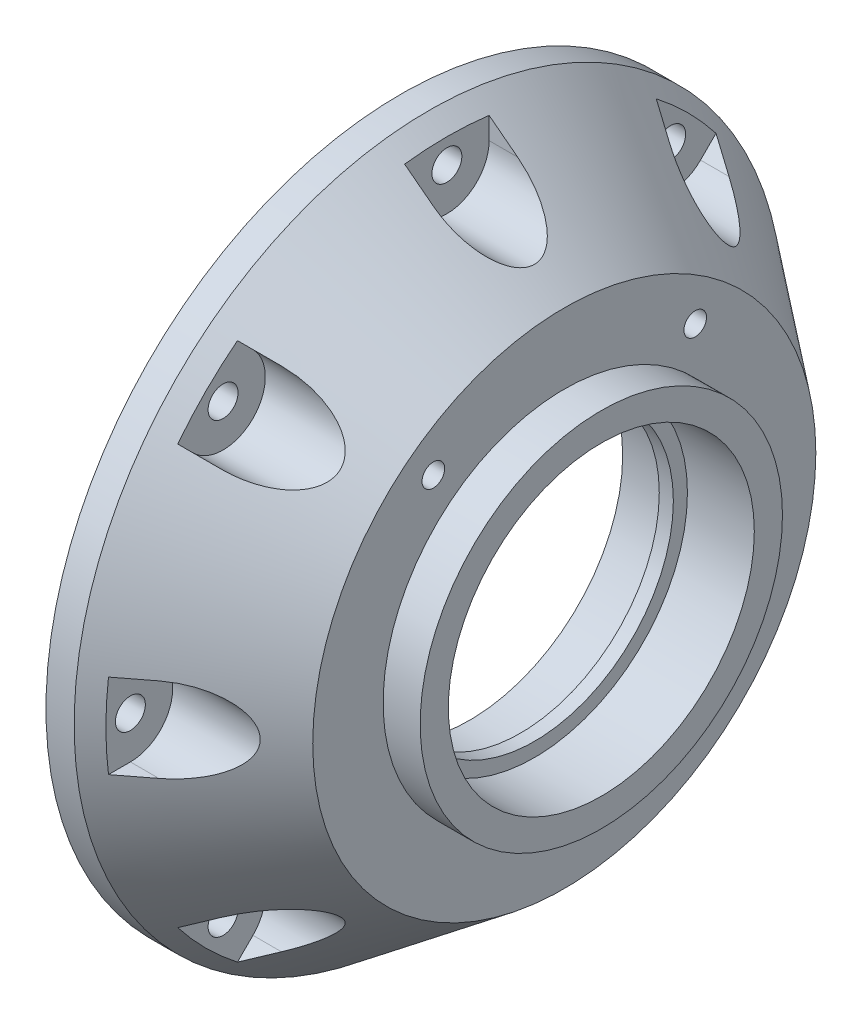
SolidWorks part; units mm, degrees
material "6061-T6 (SS)"
ref_plane "Front" through (0, 0, 0) normal (0, 0, 1) x (1, 0, 0)
ref_plane "Top" through (0, 0, 0) normal (0, 1, 0) x (1, 0, 0)
ref_plane "Right" through (0, 0, 0) normal (1, 0, 0) x (0, 0, -1)
sketch "Sketch1" plane through (0, 0, 0) normal (0, 0, 1) x (1, 0, 0)
  line L0 (462.4789, 312.41) -> (468.8289, 312.41)
  line L1 (462.4789, 312.41) -> (462.4789, 294.26)
  line L2 (462.4789, 152.41) -> (462.4789, 312.41) construction
  line L3 (462.4789, 294.26) -> (478.0364, 294.26)
  line L4 (478.0364, 294.26) -> (478.0364, 266.9159)
  line L5 (478.0364, 266.9159) -> (489.4664, 266.9159)
  line L6 (489.4664, 266.9159) -> (489.4664, 263.7409)
  line L7 (489.4664, 263.7409) -> (492.6414, 263.7409)
  line L8 (492.6414, 263.7409) -> (492.6414, 266.9159)
  line L9 (492.6414, 266.9159) -> (507.7239, 266.9159)
  line L10 (507.7239, 266.9159) -> (507.7239, 273.2659)
  line L11 (470.4164, 178.435) -> (470.4164, 286.385) construction
  line L12 (507.7239, 273.2659) -> (499.3724, 273.2659)
  line L13 (499.3724, 273.2659) -> (499.3724, 289.1409)
  line L14 (468.8289, 312.41) -> (499.3724, 289.1409)
  line L18 (596.9, 232.41) -> (-596.9, 232.41) construction
  line L19 (499.3724, 289.1409) -> (499.3724, 314.579) construction
  line L20 (462.4789, 294.2592) -> (462.4789, 294.2608) construction
  line L21 (596.9, 232.41) -> (-596.9, 232.41)
  line L22 (499.3724, 314.579) -> (505.7224, 314.579) construction
  line L23 (505.7224, 314.579) -> (505.7224, 288.4866) construction
  line L24 (499.3724, 306.07) -> (499.3724, 300.1695) construction
  line L25 (516.6952, 314.579) -> (499.3724, 314.579) construction
  line L28 (507.7239, 232.41) -> (507.7239, 266.3444) construction
  line L29 (492.6414, 264.6299) -> (492.6414, 232.41) construction
  line L30 (489.4664, 232.41) -> (489.4664, 264.6299) construction
  line L40 (487.1804, 266.9159) -> (474.9553, 266.9159) construction
  line L48 (507.1524, 266.9159) -> (494.9274, 266.9159) construction
  dimension "D2" = 7.62
  dimension "D1" = 6.35
  dimension "D3" = 3.175
  dimension "D4" = 6.35
  dimension "D5" = 6.35
  dimension "D6" = 15.875
revolve "Revolve1" add sketch "Sketch1" angle 360 about L21
fillet "Fillet1" radius 9.525 1 edges at (478.0364, 232.41, -61.85)
sketch "Sketch3" plane through (462.4789, 0, 0) normal (-1, 0, 0) x (0, 0, 1)
  line L0 (9.525, 303.785) -> (9.525, 311.8409)
  line L1 (0, 232.41) -> (0, 310.2008) construction
  line L2 (57.2049, 276.1445) -> (62.9013, 281.841)
  line L3 (43.7345, 289.6149) -> (49.431, 295.3113)
  line L4 (71.375, 222.885) -> (79.4309, 222.885)
  line L5 (71.375, 241.935) -> (79.4309, 241.935)
  line L6 (43.7345, 175.2051) -> (49.431, 169.5087)
  line L7 (57.2049, 188.6755) -> (62.9013, 182.979)
  line L8 (5.5562, 300.5771) -> (5.5562, 306.9929) construction
  line L9 (5.5562, 306.9929) -> (0, 310.2008) construction
  line L10 (0, 310.2008) -> (-5.5563, 306.9929) construction
  line L11 (-5.5563, 306.9929) -> (-5.5563, 300.5771) construction
  line L12 (-5.5563, 300.5771) -> (0, 297.3692) construction
  line L13 (0, 297.3692) -> (5.5562, 300.5771) construction
  line L14 (-9.525, 161.035) -> (-9.525, 152.9791)
  line L15 (-9.525, 303.785) -> (-9.525, 311.8409)
  line L16 (9.525, 161.035) -> (9.525, 152.9791)
  line L17 (-57.2049, 188.6755) -> (-62.9013, 182.979)
  line L18 (-43.7345, 175.2051) -> (-49.431, 169.5087)
  line L19 (-71.375, 241.935) -> (-79.4309, 241.935)
  line L20 (-71.375, 222.885) -> (-79.4309, 222.885)
  line L21 (-43.7345, 289.6149) -> (-49.431, 295.3113)
  line L22 (-57.2049, 276.1445) -> (-62.9013, 281.841)
  arc A0 (43.7345, 289.6149) -> (57.2049, 276.1445) centre (50.4697, 282.8797) ccw
  arc A1 (71.375, 241.935) -> (71.375, 222.885) centre (71.375, 232.41) ccw
  arc A2 (57.2049, 188.6755) -> (43.7345, 175.2051) centre (50.4697, 181.9403) ccw
  arc A3 (9.525, 161.035) -> (-9.525, 161.035) centre (0, 161.035) ccw
  arc A4 (-43.7345, 175.2051) -> (-57.2049, 188.6755) centre (-50.4697, 181.9403) ccw
  circle A5 centre (0, 303.785) radius 5.5563 construction
  arc A6 (-71.375, 222.885) -> (-71.375, 241.935) centre (-71.375, 232.41) ccw
  arc A7 (-9.525, 303.785) -> (9.525, 303.785) centre (0, 303.785) ccw
  arc A8 (-57.2049, 276.1445) -> (-43.7345, 289.6149) centre (-50.4697, 282.8797) ccw
  circle A9 centre (0, 232.41) radius 80 construction
  circle A10 centre (0, 232.41) radius 61.85 construction
  circle A12 centre (0, 303.785) radius 6.4158 construction
  point P7 (0, 303.785)
  point P17 (0, 232.41)
  point P48 (0, 232.41)
  point P59 (0, 232.41)
  point P71 (0, 232.41)
  dimension "D1" = 8
  dimension "D2" = 71.375
  dimension "D9" = 19.05
  dimension "D7" = 11.1125
extrude "Cut-Extrude1" cut sketch "Sketch3" against normal through all from offset 10.414 offset against normal yes
hole_wizard "1/4 Clearance Hole1" positions "Sketch4" profile "Sketch6" hole size "1/4" standard "ANSI Inch" end condition through all
sketch "Sketch4" plane through (462.4789, 0, 0) normal (-1, 0, 0) x (0, 0, 1)
  arc A0 (-9.525, 303.785) -> (9.525, 303.785) centre (0, 303.785) ccw construction
  point P38 (0, 303.785)
  point P70 (50.4697, 282.8797)
  point P71 (71.375, 232.41)
  point P72 (50.4697, 181.9403)
  point P73 (0, 161.035)
  point P74 (-50.4697, 181.9403)
  point P75 (-71.375, 232.41)
  point P76 (-50.4697, 282.8797)
  point P77 (0, 232.41)
  dimension "D1" = 8
sketch "Sketch6" plane through (462.4789, 303.785, 0) normal (0, 1, 0) x (0, 0, 1)
  line L0 (0, 0) -> (0, 45.245)
  line L1 (0, 45.245) -> (3.3782, 45.245)
  line L2 (3.3782, 45.245) -> (3.3782, 0)
  line L5 (3.3782, 0) -> (0, 0)
  line L11 (0, -6.35) -> (0, 107.95) construction
  dimension "Thru Hole Dia." = 6.7564
  dimension "Thru Hole Depth" = 45.245
sketch "Sketch7" plane through (499.3724, 0, 0) normal (1, 0, 0) x (0, 0, -1)
  line L1 (16.637, 289.1409) -> (-16.637, 289.1409)
  line L2 (-37.465, 271.2549) -> (-37.465, 306.07)
  line L3 (37.465, 271.2549) -> (37.465, 306.07)
  line L4 (-22.987, 306.07) -> (-22.987, 295.4909)
  line L5 (22.987, 295.4909) -> (22.987, 306.07)
  line L6 (0, 289.1409) -> (0, 273.9389) construction
  circle A0 centre (30.226, 306.07) radius 4.064 construction
  circle A1 centre (-30.226, 306.07) radius 4.064 construction
  circle A2 centre (30.226, 306.07) radius 4.064
  circle A3 centre (-30.226, 306.07) radius 4.064
  arc A4 (37.465, 271.2549) -> (24.7241, 264.9357) centre (29.5275, 271.2549) cw
  circle A5 centre (0, 232.41) radius 40.8559 construction
  circle A6 centre (-30.226, 306.07) radius 7.239
  circle A7 centre (30.226, 306.07) radius 7.239
  arc A8 (-16.637, 289.1409) -> (-22.987, 295.4909) centre (-16.637, 295.4909) cw
  arc A9 (16.637, 289.1409) -> (22.987, 295.4909) centre (16.637, 295.4909) ccw
  circle A10 centre (0, 232.41) radius 40.8559 construction
  arc A11 (24.7241, 264.9357) -> (-24.7241, 264.9357) centre (0, 232.41) ccw
  circle A12 centre (0, 232.41) radius 48.7934 construction
  arc A13 (-37.465, 271.2549) -> (-24.7241, 264.9357) centre (-29.5275, 271.2549) ccw
  circle A14 centre (0, 232.41) radius 56.7309 construction
  point P11 (0, 273.9389)
  point P15 (39.0707, 244.3551)
  point P32 (0, 289.1409)
  point P36 (0, 281.5399)
  point P38 (0, 281.5399)
  dimension "D3" = 6.35
  dimension "D4" = 7.9375
  dimension "D2" = 3.175
hole_wizard "1/4-20 Tapped Hole1" positions "3DSketch1" profile "Sketch8" tap size "1/4-20" standard "ANSI Inch"
sketch3d "3DSketch1"
  point P0 (499.3724, 271.2549, 29.5275)
  point P2 (499.3724, 271.2549, -29.5275)
sketch "Sketch8" plane through (499.3724, 271.2549, 29.5275) normal (0, 1, 0) x (0, 0, -1)
  line L0 (0, 0) -> (0, 18.0438)
  line L1 (0, 18.0438) -> (2.5527, 16.51)
  line L2 (2.5527, 16.51) -> (2.5527, 0)
  line L5 (2.5527, 0) -> (0, 0)
  line L10 (0, 18.0438) -> (-2.5527, 16.51) construction
  line L11 (0, -6.35) -> (0, 107.95) construction
  dimension "Tap Drill Dia." = 5.1054
  dimension "Tap Drill Depth" = 16.51
  dimension "Drill Angle" = 118
cosmetic thread "Hole Thread1" parameters "D1"=12.7, "D2"=6.35
cosmetic thread "Hole Thread2" parameters "D1"=12.7, "D2"=6.35
hole_wizard "3/16 (0.1875) Dowel Hole1" positions "Sketch9" profile "Sketch10" hole size "3/16" standard "ANSI Inch"
sketch "Sketch9" plane through (462.4789, 0, 0) normal (-1, 0, 0) x (0, 0, 1)
  point P0 (-27.314, 166.4681)
  point P3 (27.314, 298.3519)
sketch "Sketch10" plane through (462.4789, 166.4681, -27.314) normal (0, 1, 0) x (0, 0, 1)
  line L0 (0, 0) -> (0, 11.8448)
  line L1 (0, 11.8448) -> (2.3812, 10.414)
  line L2 (2.3812, 10.414) -> (2.3812, 0)
  line L5 (2.3812, 0) -> (0, 0)
  line L10 (0, 11.8448) -> (-2.3813, 10.414) construction
  line L11 (0, -6.35) -> (0, 107.95) construction
  dimension "Hole Dia." = 4.7625
  dimension "Hole Depth" = 10.414
  dimension "Drill Angle" = 118
